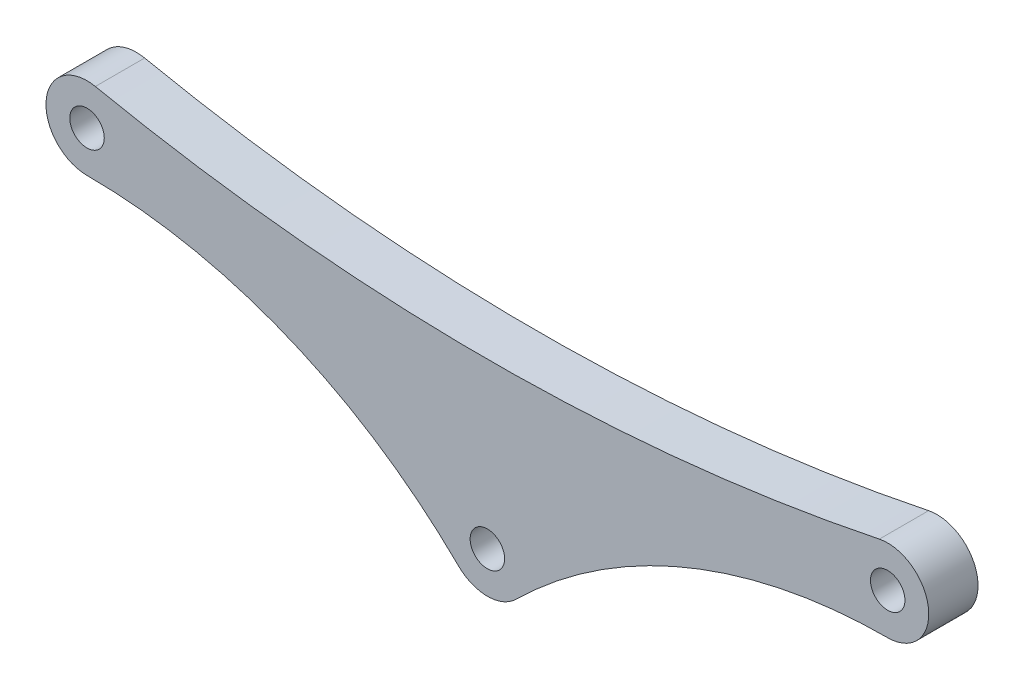
SolidWorks part; units mm, degrees
ref_plane "Front Plane" through (0, 0, 0) normal (0, 0, 1) x (1, 0, 0)
ref_plane "Top Plane" through (0, 0, 0) normal (0, 1, 0) x (1, 0, 0)
ref_plane "Right Plane" through (0, 0, 0) normal (1, 0, 0) x (0, 0, -1)
sketch "Sketch1" plane through (0, 0, 0) normal (0, 0, 1) x (1, 0, 0)
  line L0 (-48.75, 20) -> (48.75, 20) construction
  line L1 (0, 20) -> (0, 0) construction
  line L2 (0, 0) -> (0, -5) construction
  circle A0 centre (0, 0) radius 2.1
  arc A1 (3.5115, -3.5594) -> (48.75, 15) centre (48.75, -49.4141) cw
  circle A2 centre (-48.75, 20) radius 2.1
  arc A3 (47.735, 24.8959) -> (48.75, 15) centre (48.75, 20) cw
  arc A4 (-47.735, 24.8959) -> (-48.75, 15) centre (-48.75, 20) ccw
  arc A5 (-3.5115, -3.5594) -> (3.5115, -3.5594) centre (0, 0) ccw
  arc A6 (-3.5115, -3.5594) -> (-48.75, 15) centre (-48.75, -49.4141) ccw
  arc A7 (-47.735, 24.8959) -> (47.735, 24.8959) centre (0, 255.1562) ccw
  circle A8 centre (48.75, 20) radius 2.1
  dimension "D1" = 4.2
  dimension "D2" = 48.75
  dimension "D4" = 10
extrude "Boss-Extrude1" add sketch "Sketch1" along normal blind 6
